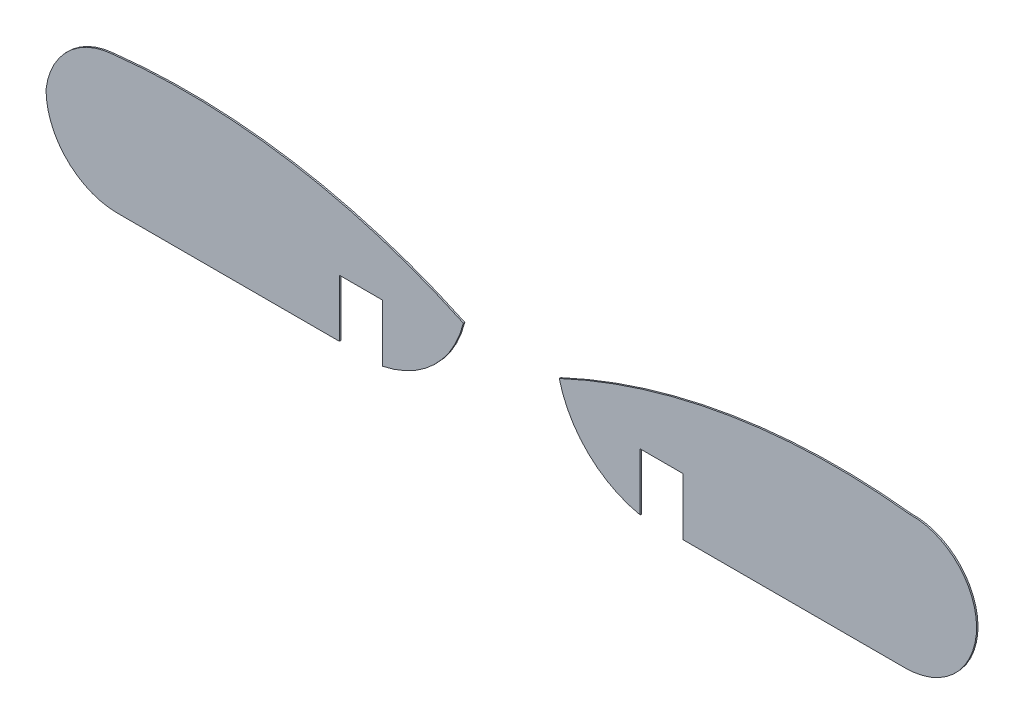
SolidWorks part; units mm, degrees
ref_plane "Alzado" through (0, 0, 0) normal (0, 0, 1) x (1, 0, 0)
ref_plane "Planta" through (0, 0, 0) normal (0, 1, 0) x (1, 0, 0)
ref_plane "Vista lateral" through (0, 0, 0) normal (1, 0, 0) x (0, 0, -1)
sketch "Model" plane through (0, 0, 0) normal (0, 0, 1) x (1, 0, 0)
  line L0 (14.2981, -28.7403) -> (14.2981, -32.7403)
  line L1 (11.2981, -28.7403) -> (14.2981, -28.7403)
  line L2 (11.2981, -32.7403) -> (11.2981, -28.7403)
  line L3 (-4.202, -32.7403) -> (11.2981, -32.7403)
  line L4 (35.2981, -32.7403) -> (50.7982, -32.7403)
  line L5 (35.2981, -28.7403) -> (35.2981, -32.7403)
  line L6 (32.2981, -28.7403) -> (35.2981, -28.7403)
  line L7 (32.2981, -32.7403) -> (32.2981, -28.7403)
  arc A0 (14.2981, -32.7403) -> (19.9494, -27.3084) centre (12.8199, -25.5466) ccw
  arc A1 (-9.202, -27.7401) -> (-4.202, -32.7403) centre (-4.202, -27.7403) ccw
  arc A2 (-4.5372, -23.2863) -> (-9.202, -27.7401) centre (-4.1526, -28.3589) ccw
  arc A3 (50.7982, -32.7403) -> (55.686, -28.7934) centre (50.7982, -27.7403) ccw
  arc A4 (26.6468, -27.3084) -> (32.2981, -32.7403) centre (33.7763, -25.5466) ccw
  arc A5 (55.686, -28.7934) -> (51.1333, -23.2863) centre (51.2863, -27.7952) ccw
  arc A6 (51.1333, -23.2863) -> (26.6468, -27.3084) centre (46.0009, -68.5881) ccw
  arc A7 (19.9494, -27.3084) -> (-4.5372, -23.2863) centre (0.5953, -68.5881) ccw
extrude "Saliente-Extruir1" add sketch "Model" along normal blind 0.1
